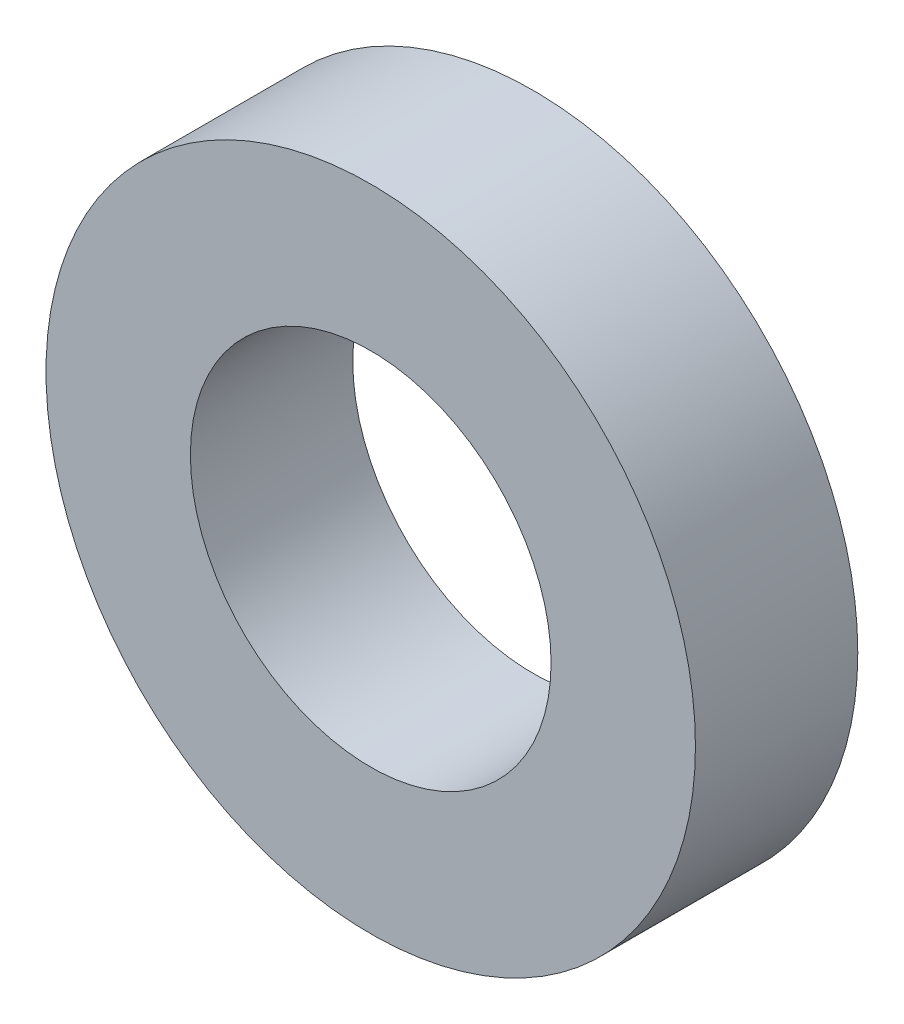
SolidWorks part; units mm, degrees
material "Ст 3 ГОСТ 380-88"
ref_plane "Спереди" through (0, 0, 0) normal (0, 0, 1) x (1, 0, 0)
ref_plane "Сверху" through (0, 0, 0) normal (0, 1, 0) x (1, 0, 0)
ref_plane "Справа" through (0, 0, 0) normal (1, 0, 0) x (0, 0, -1)
sketch "Эскиз1" plane through (0, 0, 0) normal (0, 0, 1) x (1, 0, 0)
  circle A0 centre (0, 0) radius 100
  dimension "D1" = 200
extrude "Бобышка-Вытянуть1" add sketch "Эскиз1" along normal blind 50
sketch "Эскиз2" plane through (0, 0, 50) normal (0, 0, 1) x (1, 0, 0)
  circle A0 centre (0, 0) radius 55.5382
extrude "Вырез-Вытянуть1" cut sketch "Эскиз2" against normal through all
